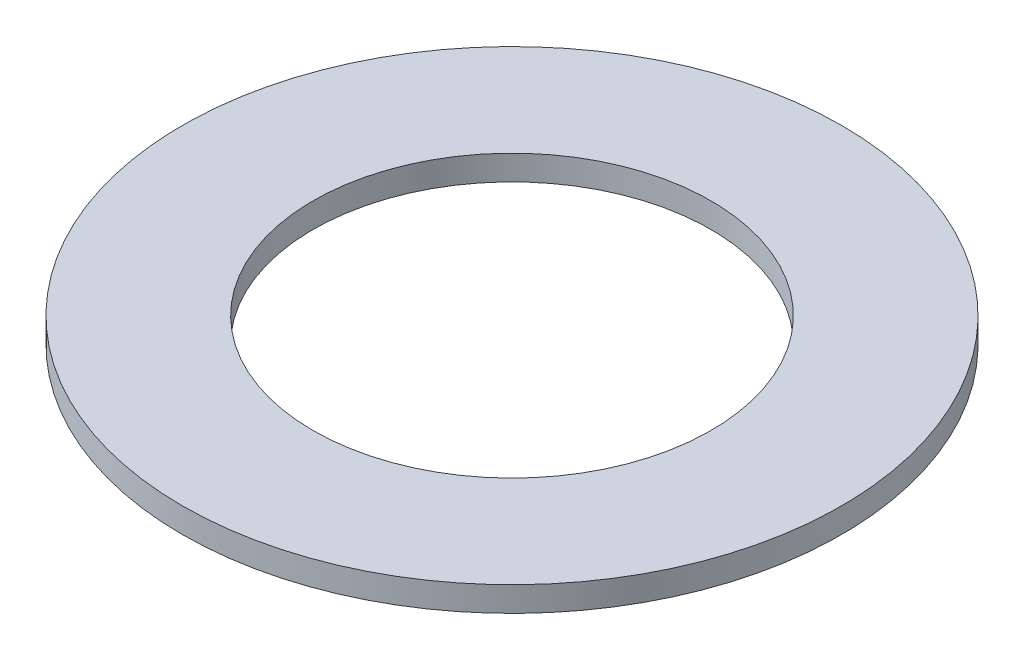
SolidWorks part; units mm, degrees
material "ﾎﾟﾘｳﾚﾀﾝ(POLYURETHANE) (11671)"
ref_plane "正面" through (0, 0, 0) normal (0, 0, 1) x (1, 0, 0)
ref_plane "平面" through (0, 0, 0) normal (0, 1, 0) x (1, 0, 0)
ref_plane "右側面" through (0, 0, 0) normal (1, 0, 0) x (0, 0, -1)
sketch "ｽｹｯﾁ1" plane through (0, 0, 0) normal (0, 1, 0) x (1, 0, 0)
  circle A0 centre (0, 0) radius 13.25
  circle A1 centre (0, 0) radius 8
  dimension "D1" = 26.5
  dimension "D2" = 16
extrude "ﾎﾞｽ - 押し出し2" add sketch "ｽｹｯﾁ1" along normal blind 1
